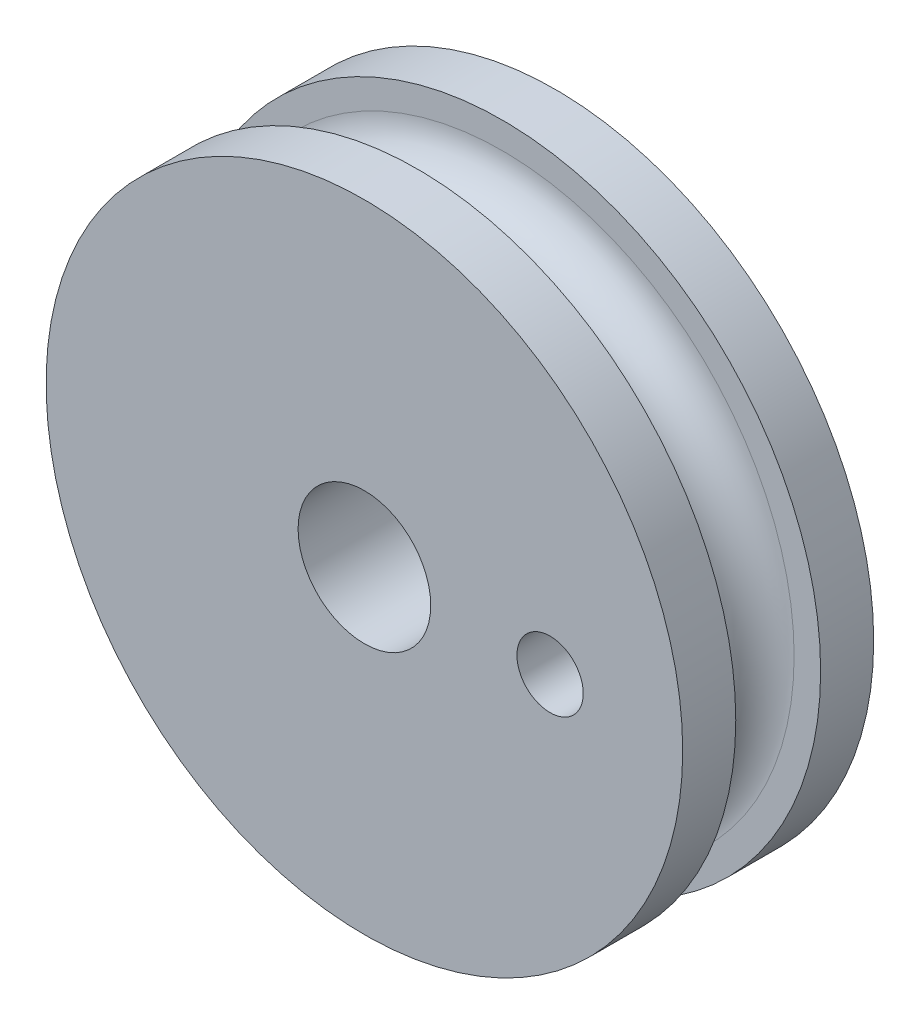
SolidWorks part; units mm, degrees
ref_plane "正面" through (0, 0, 0) normal (0, 0, 1) x (1, 0, 0)
ref_plane "平面" through (0, 0, 0) normal (0, 1, 0) x (1, 0, 0)
ref_plane "右側面" through (0, 0, 0) normal (1, 0, 0) x (0, 0, -1)
sketch "ｽｹｯﾁ1" plane through (0, 0, 0) normal (0, 0, 1) x (1, 0, 0)
  circle A0 centre (0, 0) radius 12
  dimension "D1" = 24
extrude "ﾎﾞｽ - 押し出し1" add sketch "ｽｹｯﾁ1" along normal blind 2 contours A0
sketch "ｽｹｯﾁ2" plane through (0, 0, 2) normal (0, 0, 1) x (1, 0, 0)
  circle A0 centre (0, 0) radius 11
  dimension "D1" = 22
extrude "ﾎﾞｽ - 押し出し2" add sketch "ｽｹｯﾁ2" along normal blind 3.2
sketch "ｽｹｯﾁ3" plane through (0, 0, 5.2) normal (0, 0, 1) x (1, 0, 0)
  circle A0 centre (0, 0) radius 12
  dimension "D1" = 24
extrude "ﾎﾞｽ - 押し出し3" add sketch "ｽｹｯﾁ3" along normal blind 2 contours A0
sketch "ｽｹｯﾁ4" plane through (0, 0, 0) normal (0, 0, -1) x (-1, 0, 0)
  circle A0 centre (0, 0) radius 2.5
  dimension "D1" = 5
extrude "ｶｯﾄ - 押し出し1" cut sketch "ｽｹｯﾁ4" against normal blind 30
sketch "ｽｹｯﾁ5" plane through (0, 0, 0) normal (0, 0, -1) x (-1, 0, 0)
  line L0 (0, 0) -> (7, 0)
  line L1 (0, 0) -> (-7, 0)
  circle A0 centre (-7, 0) radius 1.5
  circle A1 centre (7, 0) radius 1.5
  dimension "D3" = 3
  dimension "D4" = 3
  dimension "D1" = 7
  dimension "D2" = 7
sketch3d "3Dｽｹｯﾁ1"
  line L0 (11, 0, 5.2) -> (11, 0, 3.597)
  circle A0 centre (0, 0, 5.2) radius 11 construction
  circle A1 centre (11, 0, 3.597) radius 1.597
  point P4 (0, 0, 16.2)
  point P6 (11, 1.597, 3.597)
sweep "ｶｯﾄ - ｽｲｰﾌﾟ1" cut profiles "3Dｽｹｯﾁ1" path edge at (11, 0, 5.2)
hole_wizard "M3x0.5 ねじ穴1" positions "3Dｽｹｯﾁ2" profile "ｽｹｯﾁ6" tap size "M3x0.5" standard "JIS"
sketch3d "3Dｽｹｯﾁ2"
  point P0 (7, 0, 0)
sketch "ｽｹｯﾁ6" plane through (7, 0, 0) normal (1, 0, 0) x (0, 1, 0)
  line L0 (0, 0) -> (0, 9.2511)
  line L1 (0, 9.2511) -> (1.25, 8.5)
  line L2 (1.25, 8.5) -> (1.25, 0)
  line L5 (1.25, 0) -> (0, 0)
  line L10 (0, 9.2511) -> (-1.25, 8.5) construction
  line L11 (0, -6.35) -> (0, 107.95) construction
  dimension "ねじ下穴ﾄﾞﾘﾙ直径" = 2.5
  dimension "ねじ下穴ﾄﾞﾘﾙの深さ" = 8.5
  dimension "ﾄﾞﾘﾙ角度" = 118
cosmetic thread "穴のねじ山1" parameters "D1"=6, "D2"=3
